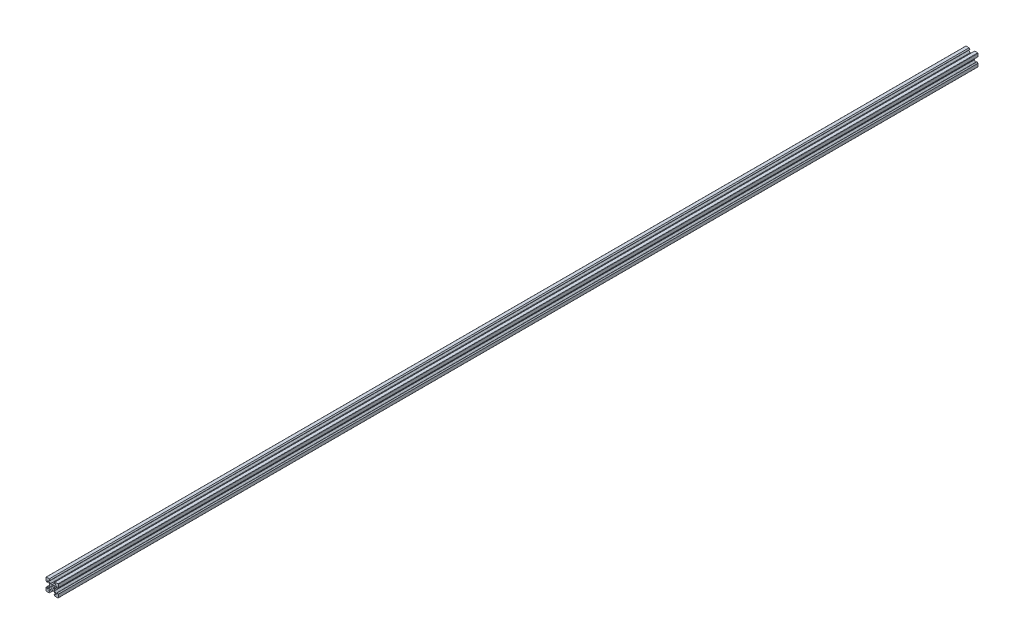
SolidWorks part; units mm, degrees
material "6061-T6 (SS)"
ref_plane "Front Plane" through (0, 0, 0) normal (0, 0, 1) x (1, 0, 0)
ref_plane "Top Plane" through (0, 0, 0) normal (0, 1, 0) x (1, 0, 0)
ref_plane "Right Plane" through (0, 0, 0) normal (1, 0, 0) x (0, 0, -1)
sketch "Sketch1" plane through (0, 0, 0) normal (0, 0, 1) x (1, 0, 0)
  line L1 (9.5, -10) -> (-9.5, -10)
  line L2 (10, -9.5) -> (10, 9.5)
  line L3 (9.5, 10) -> (-9.5, 10)
  line L4 (-10, -9.5) -> (-10, 9.5)
  line L5 (10, -10) -> (-10, 10) construction
  line L6 (10, 10) -> (-10, -10) construction
  circle A0 centre (0, 0) radius 2.1
  arc A1 (-9.5, 10) -> (-10, 9.5) centre (-9.5, 9.5) ccw
  arc A2 (10, 9.5) -> (9.5, 10) centre (9.5, 9.5) ccw
  arc A3 (9.5, -10) -> (10, -9.5) centre (9.5, -9.5) ccw
  arc A4 (-9.5, -10) -> (-10, -9.5) centre (-9.5, -9.5) cw
  point P0 (0, 0)
  line B0 (0, 0) -> (0, 10) construction
  line B1 (0, 3.69) -> (-0.21, 3.9)
  line B2 (-0.21, 3.9) -> (-2.8393, 3.9)
  line B3 (-2.8393, 3.9) -> (-5.5, 6.5607)
  line B4 (-5.5, 6.5607) -> (-5.5, 8.2)
  line B5 (-5.5, 8.2) -> (-3.125, 8.2)
  line B6 (-3.125, 8.2) -> (-3.125, 8.545)
  line B7 (-3.125, 8.545) -> (-4.58, 10)
  line B8 (-4.58, 10) -> (4.58, 10)
  line B9 (0, 0) -> (-5.9132, 5.9132) construction
  line B10 (3.125, 8.545) -> (4.58, 10)
  line B11 (3.125, 8.2) -> (3.125, 8.545)
  line B12 (5.5, 8.2) -> (3.125, 8.2)
  line B13 (5.5, 6.5607) -> (5.5, 8.2)
  line B14 (2.8393, 3.9) -> (5.5, 6.5607)
  line B15 (0.21, 3.9) -> (2.8393, 3.9)
  line B16 (0, 3.69) -> (0.21, 3.9)
  line B17 (0, 0) -> (-10, 0) construction
  line B18 (-3.69, 0) -> (-3.9, -0.21)
  line B19 (-3.9, -0.21) -> (-3.9, -2.8393)
  line B20 (-3.9, -2.8393) -> (-6.5607, -5.5)
  line B21 (-6.5607, -5.5) -> (-8.2, -5.5)
  line B22 (-8.2, -5.5) -> (-8.2, -3.125)
  line B23 (-8.2, -3.125) -> (-8.545, -3.125)
  line B24 (-8.545, -3.125) -> (-10, -4.58)
  line B25 (-10, -4.58) -> (-10, 4.58)
  line B26 (0, 0) -> (-5.9132, -5.9132) construction
  line B27 (-8.545, 3.125) -> (-10, 4.58)
  line B28 (-8.2, 3.125) -> (-8.545, 3.125)
  line B29 (-8.2, 5.5) -> (-8.2, 3.125)
  line B30 (-6.5607, 5.5) -> (-8.2, 5.5)
  line B31 (-3.9, 2.8393) -> (-6.5607, 5.5)
  line B32 (-3.9, 0.21) -> (-3.9, 2.8393)
  line B33 (-3.69, 0) -> (-3.9, 0.21)
  line B34 (0, 0) -> (0, -10) construction
  line B35 (0, -3.69) -> (0.21, -3.9)
  line B36 (0.21, -3.9) -> (2.8393, -3.9)
  line B37 (2.8393, -3.9) -> (5.5, -6.5607)
  line B38 (5.5, -6.5607) -> (5.5, -8.2)
  line B39 (5.5, -8.2) -> (3.125, -8.2)
  line B40 (3.125, -8.2) -> (3.125, -8.545)
  line B41 (3.125, -8.545) -> (4.58, -10)
  line B42 (4.58, -10) -> (-4.58, -10)
  line B43 (0, 0) -> (5.9132, -5.9132) construction
  line B44 (-3.125, -8.545) -> (-4.58, -10)
  line B45 (-3.125, -8.2) -> (-3.125, -8.545)
  line B46 (-5.5, -8.2) -> (-3.125, -8.2)
  line B47 (-5.5, -6.5607) -> (-5.5, -8.2)
  line B48 (-2.8393, -3.9) -> (-5.5, -6.5607)
  line B49 (-0.21, -3.9) -> (-2.8393, -3.9)
  line B50 (0, -3.69) -> (-0.21, -3.9)
  line B51 (0, 0) -> (10, 0) construction
  line B52 (3.69, 0) -> (3.9, 0.21)
  line B53 (3.9, 0.21) -> (3.9, 2.8393)
  line B54 (3.9, 2.8393) -> (6.5607, 5.5)
  line B55 (6.5607, 5.5) -> (8.2, 5.5)
  line B56 (8.2, 5.5) -> (8.2, 3.125)
  line B57 (8.2, 3.125) -> (8.545, 3.125)
  line B58 (8.545, 3.125) -> (10, 4.58)
  line B59 (10, 4.58) -> (10, -4.58)
  line B60 (0, 0) -> (5.9132, 5.9132) construction
  line B61 (8.545, -3.125) -> (10, -4.58)
  line B62 (8.2, -3.125) -> (8.545, -3.125)
  line B63 (8.2, -5.5) -> (8.2, -3.125)
  line B64 (6.5607, -5.5) -> (8.2, -5.5)
  line B65 (3.9, -2.8393) -> (6.5607, -5.5)
  line B66 (3.9, -0.21) -> (3.9, -2.8393)
  line B67 (3.69, 0) -> (3.9, -0.21)
  dimension "D1" = 4.2
  dimension "D3" = 0.5
  dimension "D2" = 20
sketch_block_instance "V Slot 1-4"
sketch_block "V Slot 1" parameters "D1"=10, "D2"=11, "D3"=4.3, "D4"=1.8, "D5"=0.21, "D6"=45, "D7"=9.16, "D8"=1.5, "D9"=6.25
sketch_block_instance "V Slot 1-5"
sketch_block_instance "V Slot 1-6"
sketch_block_instance "V Slot 1-7"
extrude "Boss-Extrude1" add sketch "Sketch1" along normal blind 1500 contours B67 B52 B53 B54 B55 B56 B57 B58 L2 A2 L3 B10 B11 B12 B13 B14 B15 B16 B1 B2 B3 B4 B5 B6 B7 A1 L4 B27 B28 B29 B30 B31 B32 B33 B18 B19 B20 B21 B22 B23 B24 A4 L1 B44 B45 B46 B47 B48 B49
